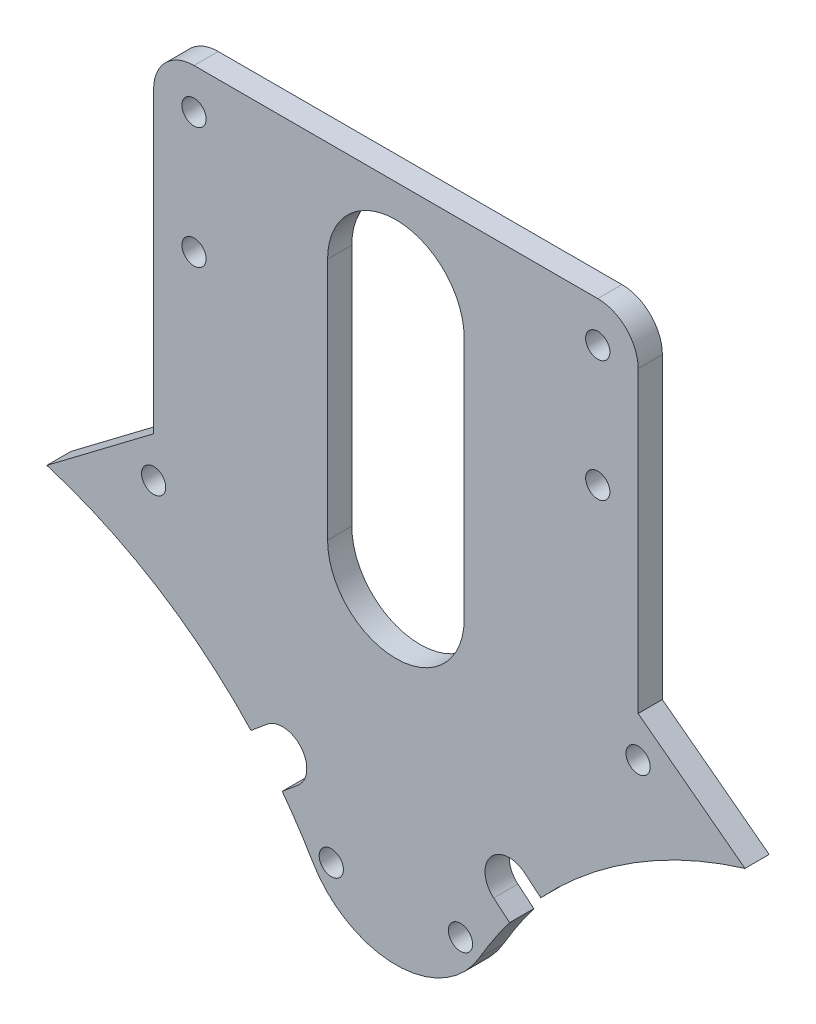
SolidWorks part; units mm, degrees
ref_plane "前视基准面" through (0, 0, 0) normal (0, 0, 1) x (1, 0, 0)
ref_plane "上视基准面" through (0, 0, 0) normal (0, 1, 0) x (1, 0, 0)
ref_plane "右视基准面" through (0, 0, 0) normal (1, 0, 0) x (0, 0, -1)
sketch "草图1" plane through (0, 0, 0) normal (0, 0, 1) x (1, 0, 0)
  line L1 (-37.42, 35) -> (37.42, 35) construction
  line L2 (30, 65) -> (43.2295, 55)
  line L3 (60, 65) -> (-60, 65) construction
  line L7 (0, 35) -> (0, 44.4384) construction
  line L8 (-30, 65) -> (-43.2295, 55)
  line L9 (30, 65) -> (30, 107)
  line L10 (20, 117) -> (-20, 117)
  line L11 (-30, 107) -> (-30, 65)
  line L12 (-60, 47) -> (60, 47) construction
  circle A0 centre (60, 0) radius 57.5 construction
  arc A1 (43.2295, 55) -> (10.3327, 28.9726) centre (60, 0) ccw
  arc A4 (-10.3327, 28.9726) -> (10.3327, 28.9726) centre (0, 35) ccw
  arc A5 (43.2295, 55) -> (59.2963, 93.7489) centre (100.7184, 53.8683) cw
  arc A6 (-43.2295, 55) -> (-10.3327, 28.9726) centre (-60, 0) cw
  arc A7 (-30, 107) -> (-20, 117) centre (-20, 107) cw
  arc A8 (20, 117) -> (30, 107) centre (20, 107) cw
  circle A15 centre (-30, 60) radius 1.5
  circle A16 centre (-8, 30) radius 1.5
  circle A17 centre (8, 30) radius 1.5
  circle A18 centre (30, 60) radius 1.5
  dimension "D1" = 60
  dimension "D4" = 10
  dimension "D2" = 10
  dimension "D3" = 70
extrude "凸台-拉伸1" add sketch "草图1" along normal blind 3
sketch "草图2" plane through (0, 0, 0) normal (0, 0, -1) x (-1, 0, 0)
  line L2 (14.0841, 34.6118) -> (12.109, 36.2691)
  line L3 (12.109, 36.2691) -> (14.0841, 34.6118) construction
  line L4 (14.0841, 34.6118) -> (14.8168, 33.84)
  line L5 (17.9408, 39.2081) -> (15.9657, 40.8654) construction
  line L6 (17.9408, 39.2081) -> (15.9657, 40.8654)
  line L7 (14.8168, 33.84) -> (18.6052, 38.3977)
  line L8 (18.6052, 38.3977) -> (17.9408, 39.2081)
  line L11 (-18.6052, 38.3977) -> (-17.9408, 39.2081)
  line L12 (-14.8168, 33.84) -> (-18.6052, 38.3977)
  line L13 (-17.9408, 39.2081) -> (-15.9657, 40.8654)
  line L14 (-14.0841, 34.6118) -> (-14.8168, 33.84)
  line L15 (-14.0841, 34.6118) -> (-12.109, 36.2691)
  arc A3 (-15.9657, 40.8654) -> (-12.109, 36.2691) centre (-14.0373, 38.5673) cw
  arc A4 (15.9657, 40.8654) -> (12.109, 36.2691) centre (14.0373, 38.5673) ccw
extrude "切除-拉伸1" cut sketch "草图2" against normal blind 10
sketch "草图3" plane through (0, 0, 0) normal (0, 0, -1) x (-1, 0, 0)
  line L0 (0, 64.3552) -> (0, 94.5) construction
  line L1 (-25, 102) -> (25, 102) construction
  line L2 (-25, 102) -> (-25, 87) construction
  line L3 (-25, 87) -> (25, 87) construction
  line L4 (25, 102) -> (25, 87) construction
  line L5 (-25, 102) -> (25, 87) construction
  line L6 (-25, 87) -> (25, 102) construction
  line L7 (-8.4589, 64.3552) -> (-8.4589, 94.5)
  line L9 (8.4589, 64.3552) -> (8.4589, 94.5)
  circle A1 centre (-25, 102) radius 1.5
  circle A2 centre (-25, 87) radius 1.5
  circle A3 centre (25, 102) radius 1.5
  circle A4 centre (25, 87) radius 1.5
  arc A5 (-8.4589, 64.3552) -> (8.4589, 64.3552) centre (0, 64.3552) ccw
  arc A6 (8.4589, 94.5) -> (-8.4589, 94.5) centre (0, 94.5) ccw
  point P0 (0, 94.5)
  point P13 (0, 79.4276)
  dimension "D3" = 3
  dimension "D4" = 3
  dimension "D5" = 3
  dimension "D6" = 3
  dimension "D1" = 50
  dimension "D2" = 15
extrude "切除-拉伸2" cut sketch "草图3" against normal blind 10
sketch "草图4" plane through (0, 0, 0) normal (0, 0, -1) x (-1, 0, 0)
  line L0 (0, 115.75) -> (0, 141.75) construction
  line L1 (-6.25, 139.5) -> (6.25, 139.5)
  line L2 (-6.25, 139.5) -> (-6.25, 117)
  line L3 (-6.25, 117) -> (6.25, 117)
  line L4 (6.25, 139.5) -> (6.25, 117)
  line L5 (-6.25, 139.5) -> (6.25, 117) construction
  line L6 (-6.25, 117) -> (6.25, 139.5) construction
  line L9 (-9.5156, 141.75) -> (-20, 117)
  line L10 (9.5156, 141.75) -> (20, 117)
  line L11 (20, 117) -> (9.5156, 117)
  line L12 (-20, 117) -> (20, 117) construction
  line L13 (-20, 117) -> (-9.5156, 117)
  line L15 (-9.5156, 117) -> (-2.8447, 108.9721)
  line L16 (-2.8447, 108.9721) -> (9.5156, 117)
  circle A0 centre (25, 102) radius 1.5 construction
  circle A2 centre (0, 141.75) radius 1
  arc A4 (9.5156, 141.75) -> (-9.5156, 141.75) centre (0, 141.75) ccw
  point P0 (0, 128.25)
  point P12 (0, 118.125)
  dimension "D5" = 2
  dimension "D7" = 13.5
  dimension "D1" = 12.5
  dimension "D2" = 22.5
  dimension "D3" = 15
extrude "凸台-拉伸2" add sketch "草图4" against normal up to surface (3 mm away) up to face at (26.5, 87, 3)
sketch "草图5" plane through (0, 0, 0) normal (0, 0, -1) x (-1, 0, 0)
  circle A0 centre (0, 114.75) radius 1
  circle A1 centre (0, 141.75) radius 1 construction
  dimension "D1" = 2
  dimension "D2" = 27
extrude "切除-拉伸3" cut sketch "草图5" against normal blind 10
fillet "圆角1" radius 10 4 edges at (9.5156, 141.75, 1.5) (-9.5156, 141.75, 1.5) (-20, 117, 1.5) (20, 117, 1.5)
sketch "草图6" plane through (0, 0, 0) normal (0, 0, -1) x (-1, 0, 0)
  line L0 (-30, 107) -> (30, 107)
  line L1 (30, 107) -> (76.1687, 160.0228)
  line L2 (76.1687, 160.0228) -> (-16.916, 154.6266)
  line L3 (-16.916, 154.6266) -> (-34.8715, 113.9905)
  line L4 (-34.8715, 113.9905) -> (-30, 107)
extrude "切除-拉伸4" cut sketch "草图6" against normal blind 10
fillet "圆角2" radius 5 2 edges at (-30, 107, 1.5) (30, 107, 1.5)
